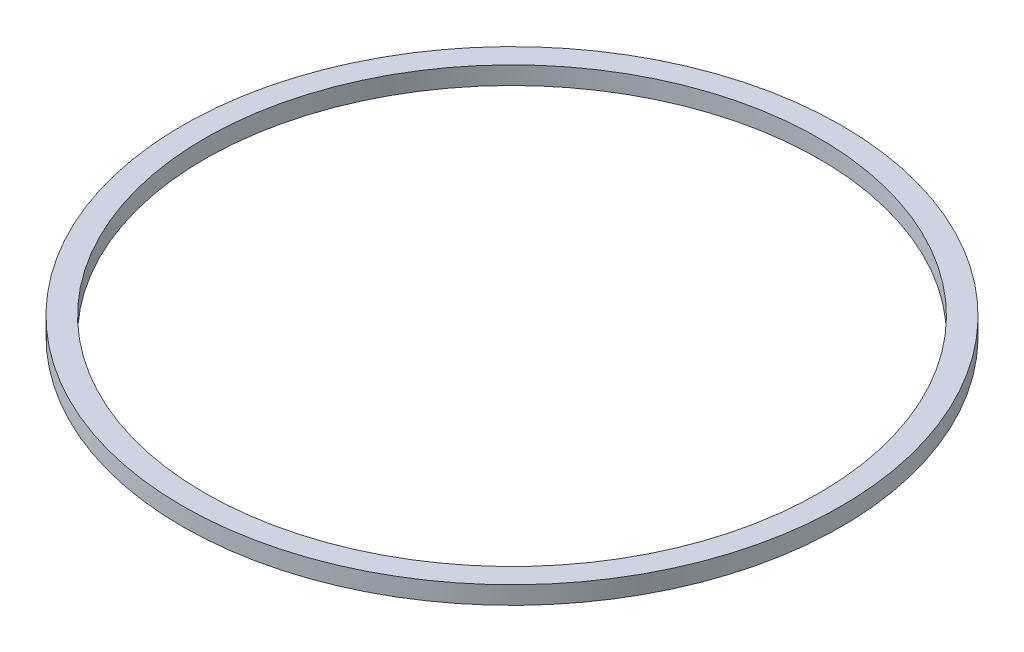
SolidWorks part; units mm, degrees
ref_plane "Front Plane" through (0, 0, 0) normal (0, 0, 1) x (1, 0, 0)
ref_plane "Top Plane" through (0, 0, 0) normal (0, 1, 0) x (1, 0, 0)
ref_plane "Right Plane" through (0, 0, 0) normal (1, 0, 0) x (0, 0, -1)
sketch "Sketch1" plane through (0, 0, 0) normal (0, 1, 0) x (1, 0, 0)
  circle A0 centre (0, 0) radius 73.75
  dimension "D1" = 147.5
extrude "Boss-Extrude1" add sketch "Sketch1" along normal blind 4
sketch "Sketch3" plane through (0, 4, 0) normal (0, 1, 0) x (1, 0, 0)
  circle A0 centre (0, 0) radius 68.75
  circle A1 centre (0, 0) radius 73.75 construction
  dimension "D1" = 5
extrude "Cut-Extrude1" cut sketch "Sketch3" against normal blind 70
